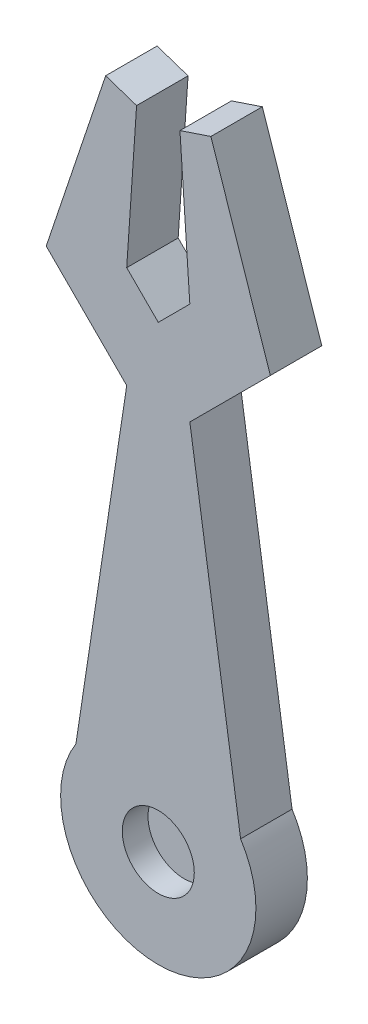
SolidWorks part; units mm, degrees
ref_plane "Front Plane" through (0, 0, 0) normal (0, 0, 1) x (1, 0, 0)
ref_plane "Top Plane" through (0, 0, 0) normal (0, 1, 0) x (1, 0, 0)
ref_plane "Right Plane" through (0, 0, 0) normal (1, 0, 0) x (0, 0, -1)
sketch "Sketch1" plane through (0, 0, 0) normal (0, 0, 1) x (1, 0, 0)
  line L1 (0, 0) -> (-15.6422, 15.6422)
  line L2 (-15.6422, 15.6422) -> (-4.0895, 50.0958)
  line L3 (-4.0895, 50.0958) -> (1.9222, 48.0801)
  line L4 (1.9222, 48.0801) -> (0, 19.8339)
  line L5 (0, 19.8339) -> (6.1342, 13.6997)
  line L6 (6.1342, 68.0895) -> (6.1342, -101.623) construction
  line L7 (12.2684, 0) -> (27.9105, 15.6422)
  line L9 (16.3578, 50.0958) -> (10.3462, 48.0801)
  line L10 (12.2684, 19.8339) -> (6.1342, 13.6997)
  line L11 (10.3462, 48.0801) -> (12.2684, 19.8339)
  line L12 (27.9105, 15.6422) -> (16.3578, 50.0958)
  line L13 (0, 0) -> (-9.8658, -65.23)
  line L14 (12.2684, 0) -> (22.1342, -65.23)
  arc A1 (-9.8658, -65.23) -> (22.1342, -65.23) centre (6.1342, -75.4312) ccw
  dimension "D1" = 16
  dimension "D2" = 16
extrude "Boss-Extrude1" add sketch "Sketch1" along normal blind 10
sketch "Sketch2" plane through (0, 0, 10) normal (0, 0, 1) x (1, 0, 0)
  circle A0 centre (6.1342, -75.4312) radius 7
extrude "Cut-Extrude1" cut sketch "Sketch2" against normal blind 5
